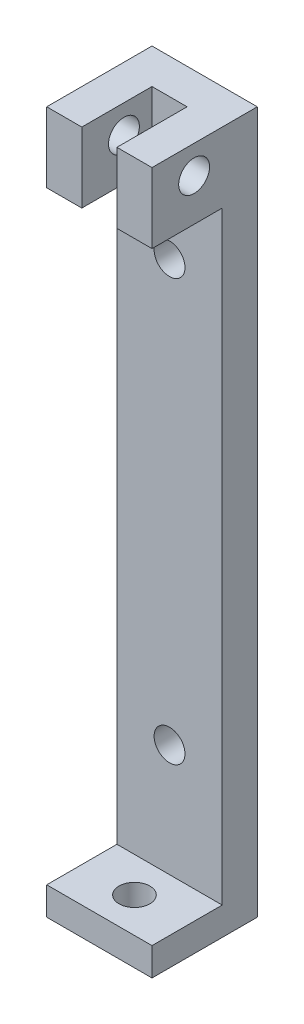
SolidWorks part; units mm, degrees
ref_plane "Ebene vorne" through (0, 0, 0) normal (0, 0, 1) x (1, 0, 0)
ref_plane "Ebene oben" through (0, 0, 0) normal (0, 1, 0) x (1, 0, 0)
ref_plane "Ebene rechts" through (0, 0, 0) normal (1, 0, 0) x (0, 0, -1)
sketch "Skizze1" plane through (0, 0, 0) normal (0, 1, 0) x (1, 0, 0)
  line L1 (-7.5, -7.5) -> (7.5, -7.5)
  line L2 (-7.5, -7.5) -> (-7.5, 7.5)
  line L3 (-7.5, 7.5) -> (7.5, 7.5)
  line L4 (7.5, -7.5) -> (7.5, 7.5)
  line L5 (-7.5, -7.5) -> (7.5, 7.5) construction
  line L6 (-7.5, 7.5) -> (7.5, -7.5) construction
  point P0 (0, 0)
  dimension "D1" = 15
  dimension "D2" = 15
extrude "Aufsatz-Linear austragen1" add sketch "Skizze1" along normal blind 4
sketch "Skizze2" plane through (0, 4, 0) normal (0, 1, 0) x (1, 0, 0)
  line L0 (7.5, -7.5) -> (7.5, 7.5) construction
  line L1 (-7.5, 7.5) -> (7.5, 7.5)
  line L2 (-7.5, 7.5) -> (-7.5, 2.5)
  line L3 (-7.5, 2.5) -> (7.5, 2.5)
  line L4 (7.5, 7.5) -> (7.5, 2.5)
  dimension "D1" = 5
extrude "Aufsatz-Linear austragen2" add sketch "Skizze2" along normal blind 96 contours L2 L1 L4 L3
sketch "Skizze3" plane through (0, 0, -2.5) normal (0, 0, 1) x (1, 0, 0)
  line L1 (-7.5, 100) -> (-2.5, 100)
  line L2 (-7.5, 100) -> (-7.5, 90)
  line L3 (-7.5, 90) -> (-2.5, 90)
  line L4 (-2.5, 100) -> (-2.5, 90)
  line L5 (7.5, 100) -> (2.5, 100)
  line L6 (7.5, 100) -> (7.5, 90)
  line L7 (7.5, 90) -> (2.5, 90)
  line L8 (2.5, 100) -> (2.5, 90)
  dimension "D1" = 5
  dimension "D2" = 10
  dimension "D3" = 5
extrude "Aufsatz-Linear austragen3" add sketch "Skizze3" along normal blind 10
sketch "Skizze4" plane through (0, 4, 0) normal (0, 1, 0) x (1, 0, 0)
  line L0 (7.5, -7.5) -> (7.5, 2.5) construction
  line L1 (-7.5, -7.5) -> (7.5, -7.5) construction
  circle A0 centre (0, -2.5) radius 2.2
  dimension "D3" = 4.4
  dimension "D1" = 7.5
  dimension "D2" = 5
extrude "Schnitt-Linear austragen1" cut sketch "Skizze4" against normal through all
sketch "Skizze5" plane through (7.5, 0, 0) normal (1, 0, 0) x (0, 0, -1)
  line L0 (7.5, 100) -> (-7.5, 100) construction
  line L1 (-7.5, 90) -> (-7.5, 100) construction
  circle A0 centre (-1.5, 96) radius 2.2
  dimension "D1" = 4.4
  dimension "D2" = 4
  dimension "D3" = 6
extrude "Schnitt-Linear austragen2" cut sketch "Skizze5" against normal up to next
sketch "Skizze6" plane through (-7.5, 0, 0) normal (-1, 0, 0) x (0, 0, 1)
  line L0 (7.5, 100) -> (7.5, 90) construction
  line L1 (-7.5, 100) -> (7.5, 100) construction
  circle A0 centre (1.5, 96) radius 2.2
  dimension "D1" = 4.4
  dimension "D2" = 6
  dimension "D3" = 4
extrude "Schnitt-Linear austragen3" cut sketch "Skizze6" against normal through all
sketch "Skizze7" plane through (0, 0, -2.5) normal (0, 0, 1) x (1, 0, 0)
  line L1 (-7.5, 0) -> (7.5, 0) construction
  line L2 (-2.5, 100) -> (2.5, 100) construction
  circle A0 centre (0, 20) radius 2.2
  circle A1 centre (0, 80) radius 2.2
  dimension "D1" = 4.4
  dimension "D2" = 20
  dimension "D3" = 20
extrude "Schnitt-Linear austragen4" cut sketch "Skizze7" against normal through all
